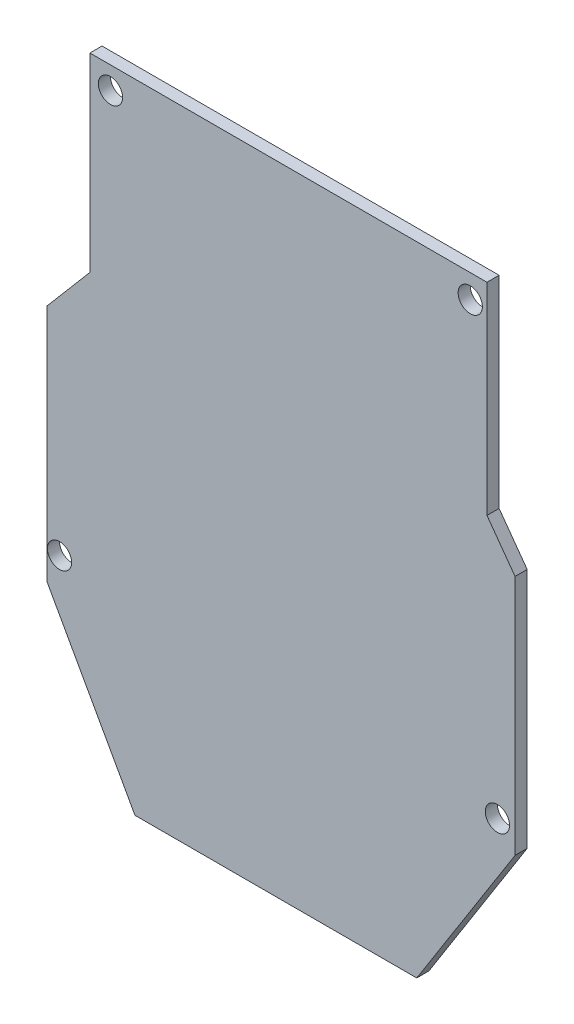
SolidWorks part; units mm, degrees
material "Silicon"
ref_plane "Front Plane" through (0, 0, 0) normal (0, 0, 1) x (1, 0, 0)
ref_plane "Top Plane" through (0, 0, 0) normal (0, 1, 0) x (1, 0, 0)
ref_plane "Right Plane" through (0, 0, 0) normal (1, 0, 0) x (0, 0, -1)
sketch "Sketch1" plane through (0, 0, 0) normal (0, 0, 1) x (1, 0, 0)
  line L0 (-32.0234, 16.5426) -> (-24.9135, 24.9114)
  line L2 (-32.0234, 16.5426) -> (-32.0234, -22.7821)
  line L4 (45.2544, 16.5426) -> (45.2544, -23.3351)
  line L9 (-24.9135, 24.9114) -> (-24.9135, 56.2695)
  line L10 (-24.9135, 56.2695) -> (40.6168, 56.2695)
  line L11 (40.6168, 56.2695) -> (40.6168, 22.9441)
  line L12 (40.6168, 22.9441) -> (45.2544, 16.5426)
  line L13 (-32.0234, -22.7821) -> (-17.4758, -48.9682)
  line L14 (-17.4758, -48.9682) -> (29.0281, -48.9682)
  line L15 (29.0281, -48.9682) -> (45.2544, -23.3351)
  line L24 (36.3845, -12.4051) -> (36.51, -12.4051) construction
  circle A11 centre (-21.5227, 52.6011) radius 2
  circle A12 centre (37.8556, 52.3886) radius 2
  circle A13 centre (42.3407, -19.5084) radius 2
  circle A14 centre (-29.9294, -18.0638) radius 2
  point P16 (0, 0)
  point P18 (0, 0)
  point P20 (0, 0)
  point P21 (36.3845, 52.8996)
  point P22 (-22.4595, 52.8996)
  point P23 (0, 0)
  point P24 (40.4853, 56.2695)
  point P25 (0, 0)
  point P26 (37.8556, 52.3886)
  point P27 (0, 0)
  point P28 (-24.7168, 25.1784)
  point P29 (-32.0234, 16.5426)
  point P30 (-29.9294, -18.0638)
  point P31 (-17.7346, -48.5024)
  point P32 (29.0281, -48.9682)
  point P33 (45.0496, -23.6586)
  point P34 (0, 0)
  point P35 (45.2544, 16.5426)
  point P36 (40.6168, 22.9441)
  point P37 (0, 0)
  point P38 (0, 0)
  point P39 (0, 0)
  point P40 (-24.9135, 24.9114)
extrude "Boss-Extrude1" add sketch "Sketch1" along normal blind 2
